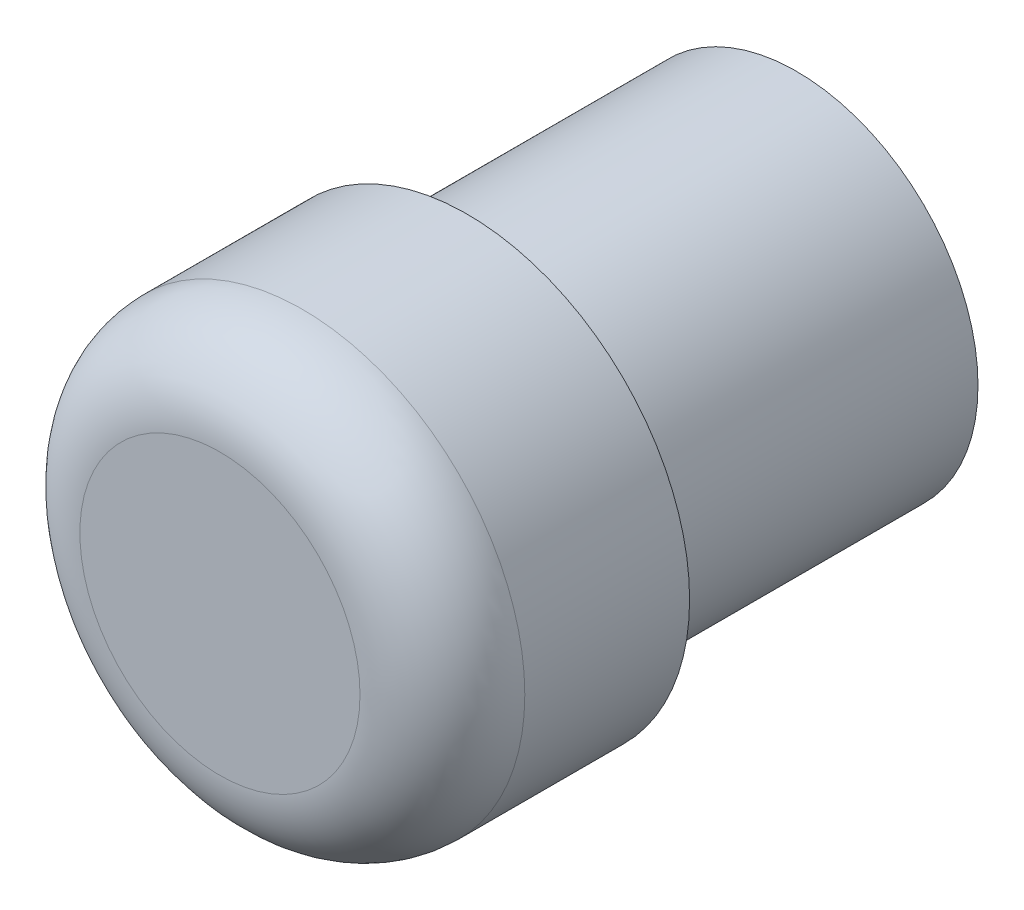
SolidWorks part; units mm, degrees
material "6063-O"
ref_plane "前视基准面" through (0, 0, 0) normal (0, 0, 1) x (1, 0, 0)
ref_plane "上视基准面" through (0, 0, 0) normal (0, 1, 0) x (1, 0, 0)
ref_plane "右视基准面" through (0, 0, 0) normal (1, 0, 0) x (0, 0, -1)
other "Configuration Table"
sketch "草图1" plane through (0, 0, 0) normal (0, 0, 1) x (1, 0, 0)
  circle A0 centre (-173.2755, 0) radius 11
  dimension "D1" = 22
extrude "凸台-拉伸1" add sketch "草图1" along normal blind 20
sketch "草图2" plane through (0, 0, 20) normal (0, 0, 1) x (1, 0, 0)
  circle A0 centre (-173.2755, 0) radius 13.5
  circle A1 centre (-173.2755, 0) radius 11 construction
  dimension "D1" = 27
extrude "凸台-拉伸2" add sketch "草图2" along normal blind 15
fillet "圆角1" radius 5 1 edges at (-159.7755, 0, 35)
